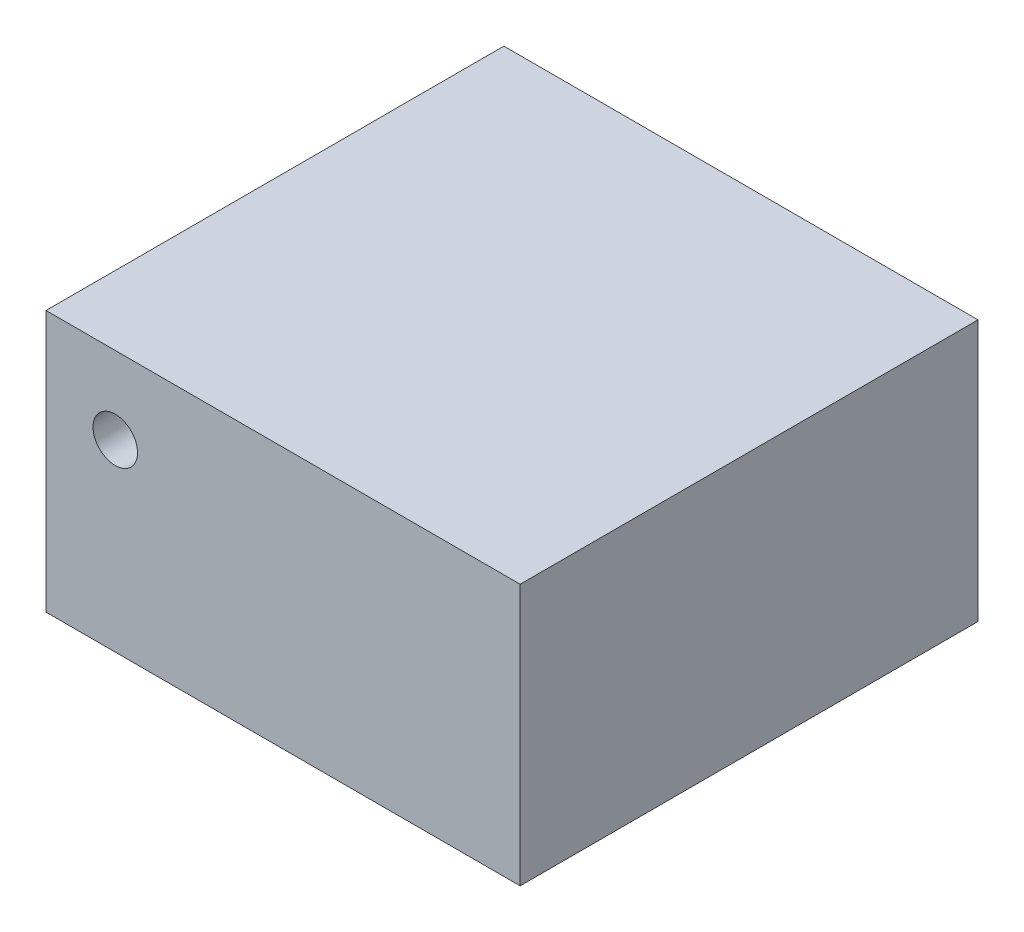
SolidWorks part; units mm, degrees
material "ABS"
ref_plane "Front" through (0, 0, 0) normal (0, 0, 1) x (1, 0, 0)
ref_plane "Top" through (0, 0, 0) normal (0, 1, 0) x (1, 0, 0)
ref_plane "Right" through (0, 0, 0) normal (1, 0, 0) x (0, 0, -1)
sketch "Sketch1" plane through (0, 0, 0) normal (0, 0, 1) x (1, 0, 0)
  line L1 (-15.5575, 8.5725) -> (15.5575, 8.5725)
  line L2 (-15.5575, 8.5725) -> (-15.5575, -8.5725)
  line L3 (-15.5575, -8.5725) -> (15.5575, -8.5725)
  line L4 (15.5575, 8.5725) -> (15.5575, -8.5725)
  line L5 (-15.5575, 8.5725) -> (15.5575, -8.5725) construction
  line L6 (-15.5575, -8.5725) -> (15.5575, 8.5725) construction
  point P0 (0, 0)
  dimension "D1" = 31.115
  dimension "D2" = 17.145
extrude "Motor Body" add sketch "Sketch1" along normal blind 30.0482
sketch "Sketch2" plane through (0, -8.5725, 0) normal (0, -1, 0) x (1, 0, 0)
  line L0 (-15.5575, 0) -> (15.5575, 0) construction
  line L1 (-0.8763, -7.4676) -> (5.5245, -7.4676)
  line L2 (-2.1463, -6.1976) -> (-2.1463, 0)
  line L3 (-2.1463, 0) -> (6.7945, 0)
  line L4 (6.7945, -6.1976) -> (6.7945, 0)
  line L5 (-2.1463, -7.4676) -> (6.7945, 0) construction
  line L6 (-2.1463, 0) -> (6.7945, -7.4676) construction
  line L7 (15.5575, 30.0482) -> (15.5575, 0) construction
  line L13 (0.6858, -5.4356) -> (3.8862, -5.4356)
  line L14 (-0.5842, -4.1656) -> (-0.5842, -3.5306)
  line L15 (0.6858, -2.2606) -> (3.8862, -2.2606)
  line L16 (5.1562, -4.1656) -> (5.1562, -3.5306)
  arc A0 (-0.8763, -7.4676) -> (-2.1463, -6.1976) centre (-0.8763, -6.1976) cw
  arc A1 (5.5245, -7.4676) -> (6.7945, -6.1976) centre (5.5245, -6.1976) ccw
  arc A2 (3.8862, -5.4356) -> (5.1562, -4.1656) centre (3.8862, -4.1656) ccw
  arc A3 (0.6858, -5.4356) -> (-0.5842, -4.1656) centre (0.6858, -4.1656) cw
  arc A4 (3.8862, -2.2606) -> (5.1562, -3.5306) centre (3.8862, -3.5306) cw
  arc A5 (-0.5842, -3.5306) -> (0.6858, -2.2606) centre (0.6858, -3.5306) cw
  point P7 (2.3241, -3.7338)
  point P21 (5.1562, -5.4356)
  point P24 (-0.5842, -5.4356)
  point P29 (-0.5842, -2.2606)
  dimension "D8" = 1.27
  dimension "D1" = 8.763
  dimension "D2" = 7.4676
  dimension "D3" = 8.9408
  dimension "D4" = 3.175
  dimension "D5" = 5.7404
  dimension "D6" = 2.032
  dimension "D7" = 1.6383
extrude "Fastening hole" add sketch "Sketch2" against normal blind 1.9812
sketch "Sketch3" plane through (0, 0, 0) normal (0, 0, -1) x (-1, 0, 0)
  line L0 (15.5575, 8.5725) -> (15.5575, -8.5725) construction
  line L1 (-15.5575, 8.5725) -> (15.5575, 8.5725) construction
  circle A0 centre (11.0109, 3.4925) radius 1.4605
  dimension "D1" = 2.921
  dimension "D2" = 4.5466
  dimension "D3" = 5.08
extrude "Shaft hole" cut sketch "Sketch3" against normal through all
